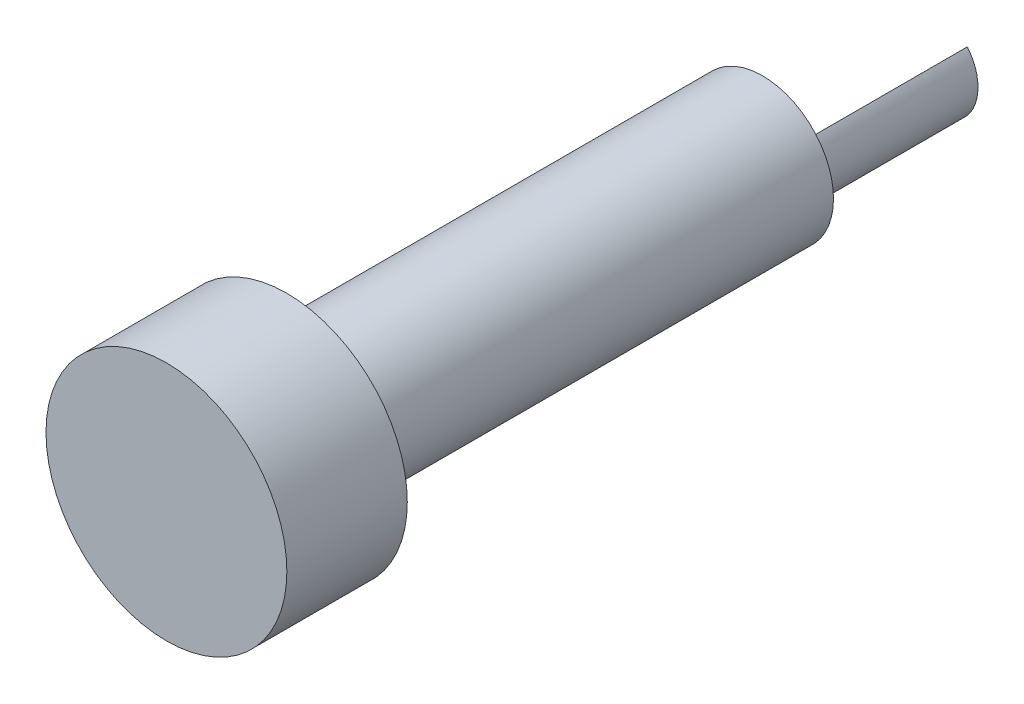
SolidWorks part; units mm, degrees
material "ABS"
ref_plane "Front Plane" through (0, 0, 0) normal (0, 0, 1) x (1, 0, 0)
ref_plane "Top Plane" through (0, 0, 0) normal (0, 1, 0) x (1, 0, 0)
ref_plane "Right Plane" through (0, 0, 0) normal (1, 0, 0) x (0, 0, -1)
sketch "Sketch5" plane through (0, 0, 0) normal (0, 0, 1) x (1, 0, 0)
  line L4 (1.525, 0) -> (1.525, 1.255)
  line L5 (1.525, -1.255) -> (1.525, 0)
  arc A0 (1.525, -1.255) -> (1.525, 1.255) centre (0, 0) ccw
extrude "Boss-Extrude1" add sketch "Sketch5" along normal blind 9.906 contours A0 L4 L5
sketch "Sketch6" plane through (0, 0, 9.906) normal (0, 0, 1) x (1, 0, 0)
  circle A0 centre (0, 0) radius 1.975
extrude "Boss-Extrude2" add sketch "Sketch6" along normal blind 17.272
sketch "Sketch7" plane through (0, 0, 27.178) normal (0, 0, 1) x (1, 0, 0)
  circle A0 centre (0, 0) radius 2.9915
extrude "Boss-Extrude3" add sketch "Sketch7" against normal blind 20.066
sketch "Sketch8" plane through (0, 0, 0) normal (0, 0, 1) x (1, 0, 0)
  line L2 (1.525, 1.255) -> (1.525, 0)
  line L3 (1.525, 0) -> (1.525, -1.255)
  line L4 (1.525, 1.255) -> (1.525, 0)
  line L5 (1.525, 0) -> (1.525, -1.255)
  arc A0 (1.525, 1.255) -> (1.525, -1.255) centre (0, 0) ccw
  arc A1 (1.525, -1.255) -> (1.525, 1.255) centre (0, 0) ccw
  dimension "D1" = 0
extrude "Cut-Extrude1" cut sketch "Sketch8" along normal blind 20.066
sketch "Sketch9" plane through (0, 0, 27.178) normal (0, 0, 1) x (1, 0, 0)
  circle A0 centre (0, 0) radius 5.08
extrude "Boss-Extrude4" add sketch "Sketch9" along normal blind 5.08
